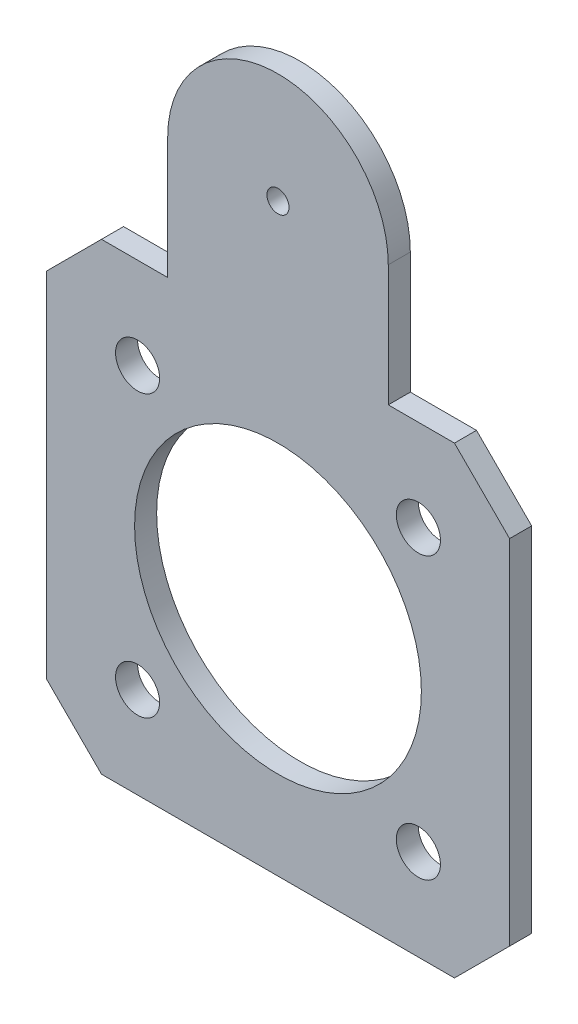
SolidWorks part; units mm, degrees
material "1023 Chapa de acero al carbono (SS)"
ref_plane "Alzado" through (0, 0, 0) normal (0, 0, 1) x (1, 0, 0)
ref_plane "Planta" through (0, 0, 0) normal (0, 1, 0) x (1, 0, 0)
ref_plane "Vista lateral" through (0, 0, 0) normal (1, 0, 0) x (0, 0, -1)
sketch "Croquis1" plane through (0, 0, 0) normal (0, 0, 1) x (1, 0, 0)
  line L0 (10, 21) -> (16, 21)
  line L1 (-16, -21) -> (16, -21)
  line L2 (-21, -16) -> (-21, 16)
  line L3 (-16, 21) -> (-10, 21)
  line L4 (21, -16) -> (21, 16)
  line L5 (-21, -21) -> (21, 21) construction
  line L6 (-21, 21) -> (21, -21) construction
  line L7 (-21, 16) -> (-16, 21)
  line L8 (16, 21) -> (21, 16)
  line L9 (16, -21) -> (21, -16)
  line L10 (-21, -16) -> (-16, -21)
  line L11 (-10, 21) -> (-10, 32)
  line L12 (10, 21) -> (10, 32)
  circle A1 centre (0, 0) radius 18 construction
  circle A2 centre (12.7279, 12.7279) radius 2
  circle A3 centre (12.7279, -12.7279) radius 2
  circle A4 centre (-12.7279, -12.7279) radius 2
  circle A5 centre (-12.7279, 12.7279) radius 2
  circle A7 centre (0, 0) radius 13
  arc A8 (10, 32) -> (-10, 32) centre (0, 32) ccw
  circle A9 centre (0, 32) radius 1
  point P0 (0, 0)
  point P11 (12.7279, 12.7279)
  point P23 (0, 0)
  dimension "D3" = 11
  dimension "D4" = 36
  dimension "D5" = 4
  dimension "D7" = 2
  dimension "D8" = 26
  dimension "D1" = 42
  dimension "D2" = 42
  dimension "D6" = 4
extrude "Saliente-Extruir1" add sketch "Croquis1" along normal blind 2
